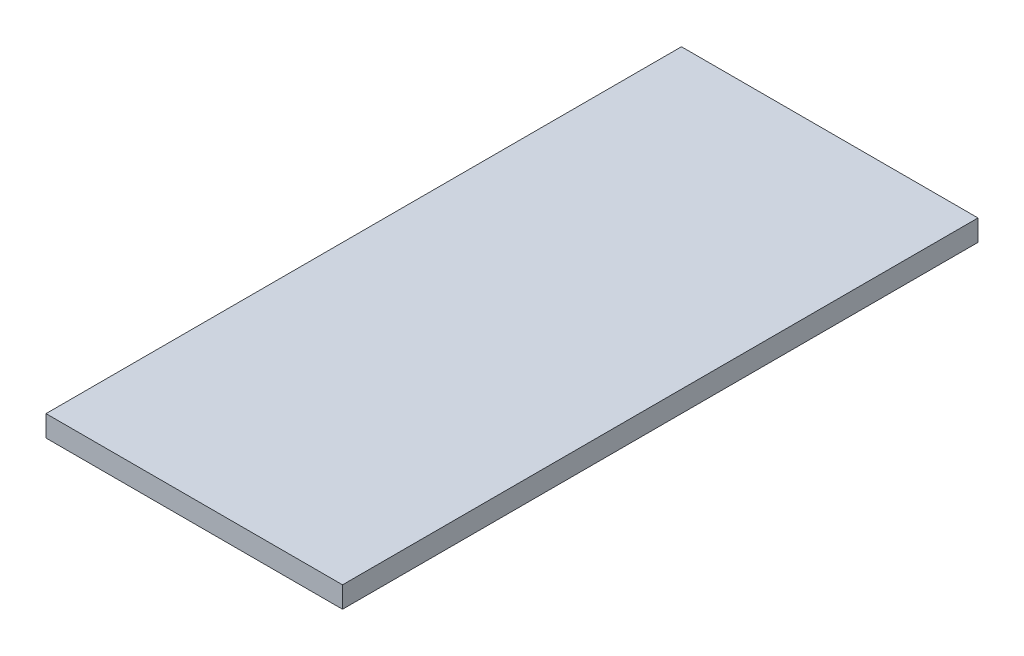
SolidWorks part; units mm, degrees
ref_plane "Front Plane" through (0, 0, 0) normal (0, 0, 1) x (1, 0, 0)
ref_plane "Top Plane" through (0, 0, 0) normal (0, 1, 0) x (1, 0, 0)
ref_plane "Right Plane" through (0, 0, 0) normal (1, 0, 0) x (0, 0, -1)
sketch "Sketch1" plane through (0, 0, 0) normal (0, 1, 0) x (1, 0, 0)
  line L1 (-43.0168, 35) -> (26.9832, 35)
  line L2 (-43.0168, 35) -> (-43.0168, -115)
  line L3 (-43.0168, -115) -> (26.9832, -115)
  line L4 (26.9832, 35) -> (26.9832, -115)
  line L5 (-43.0168, 35) -> (26.9832, -115) construction
  line L6 (-43.0168, -115) -> (26.9832, 35) construction
  point P4 (-8.0168, -40)
  dimension "D1" = 70
  dimension "D2" = 150
extrude "Boss-Extrude1" add sketch "Sketch1" along normal blind 5
